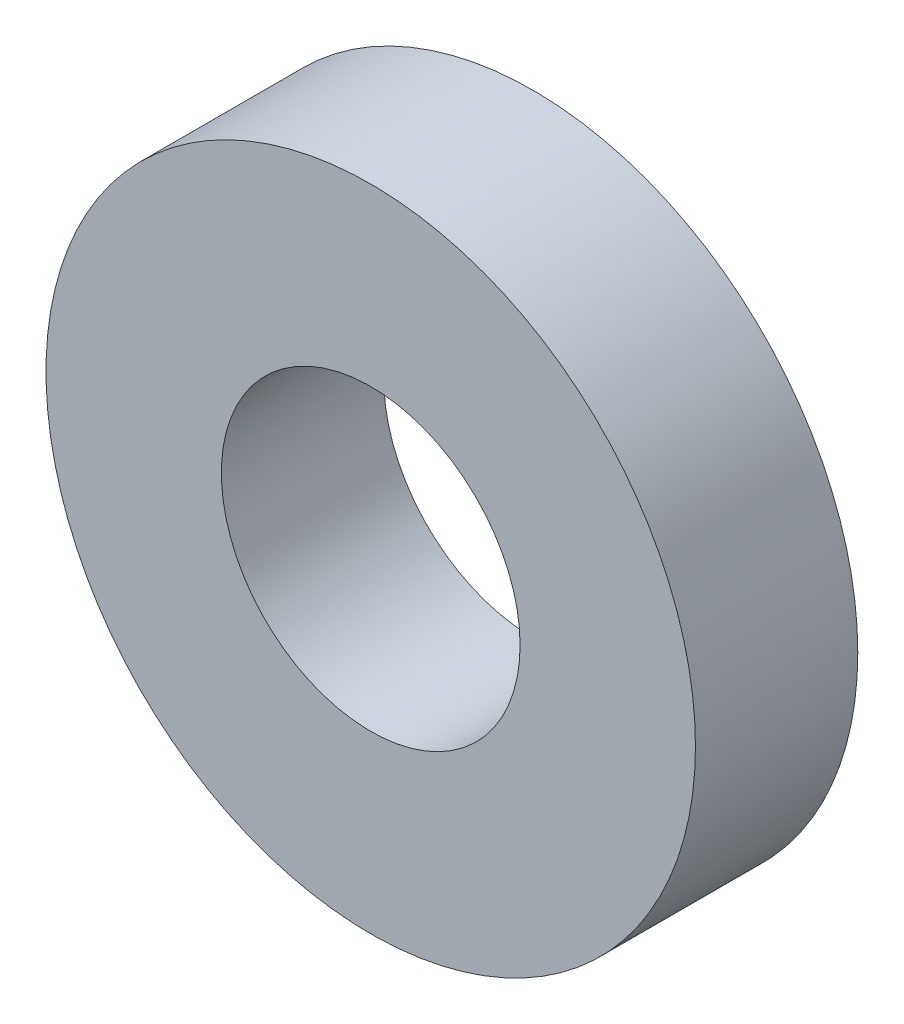
SolidWorks part; units mm, degrees
ref_plane "Front Plane" through (0, 0, 0) normal (0, 0, 1) x (1, 0, 0)
ref_plane "Top Plane" through (0, 0, 0) normal (0, 1, 0) x (1, 0, 0)
ref_plane "Right Plane" through (0, 0, 0) normal (1, 0, 0) x (0, 0, -1)
sketch "Sketch1" plane through (0, 0, 0) normal (0, 0, 1) x (1, 0, 0)
  circle A0 centre (0, 0) radius 3.175
  circle A1 centre (0, 0) radius 1.4605
  dimension "OD" = 6.35
  dimension "ID" = 2.921
extrude "Extrude1" add sketch "Sketch1" along normal mid plane 1.5875
sketch "Sketch2" plane through (0, 0, 0) normal (1, 0, 0) x (0, 0, -1)
  line L0 (-0.7937, -1.4605) -> (0.7937, -1.4605) construction
  line L3 (0.7937, 1.4605) -> (-0.7937, 1.4605) construction
  line L5 (-0.7937, -1.4605) -> (0.7937, -1.4605)
  line L6 (0.7937, 1.4605) -> (-0.7937, 1.4605)
sketch "Sketch4" plane through (0, 0, 0.7937) normal (0, 0, 1) x (1, 0, 0)
  line L0 (0, 0) -> (-1.0327, 1.0327)
  line L1 (0, -2.1828) -> (0, 2.1828) construction
  circle A0 centre (0, 0) radius 1.4605 construction
  dimension "D1" = 45
